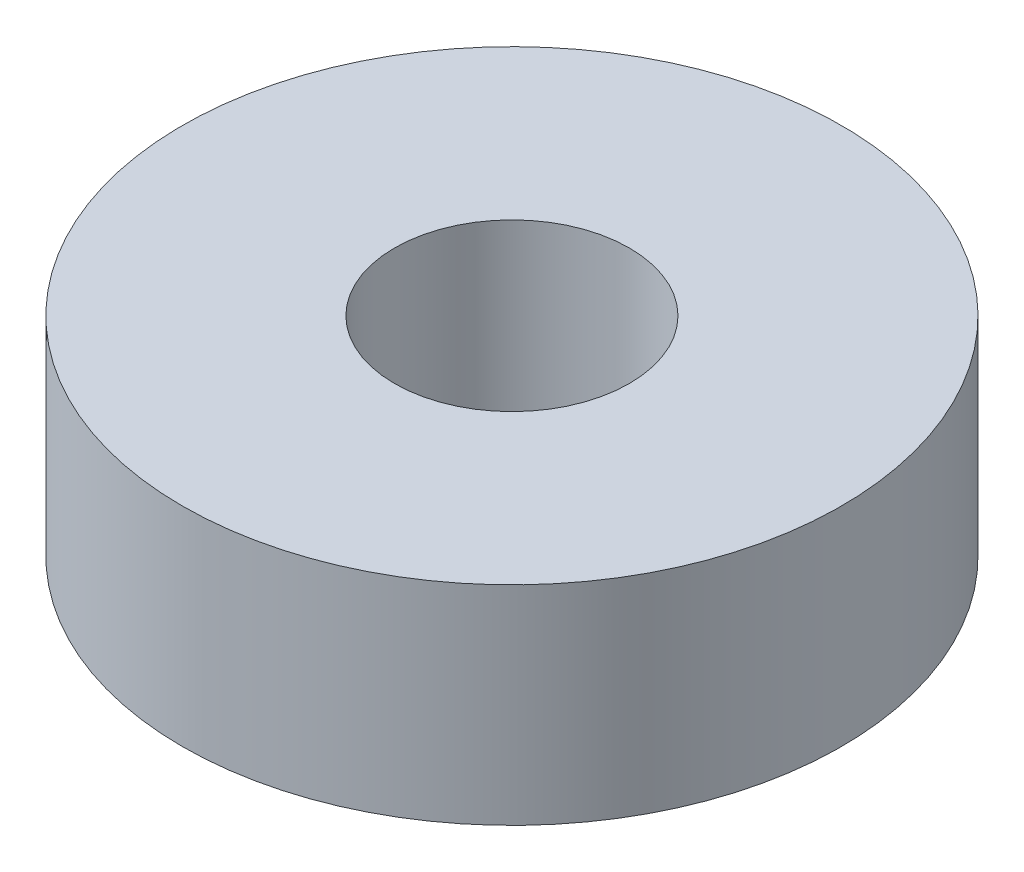
SolidWorks part; units mm, degrees
ref_plane "Front Plane" through (0, 0, 0) normal (0, 0, 1) x (1, 0, 0)
ref_plane "Top Plane" through (0, 0, 0) normal (0, 1, 0) x (1, 0, 0)
ref_plane "Right Plane" through (0, 0, 0) normal (1, 0, 0) x (0, 0, -1)
sketch "Sketch1" plane through (0, 0, 0) normal (0, 1, 0) x (1, 0, 0)
  circle A0 centre (0, 0) radius 11.049
  circle A1 centre (0, 0) radius 3.937
  dimension "D1" = 22.098
  dimension "D2" = 7.874
extrude "Boss-Extrude1" add sketch "Sketch1" along normal blind 6.985
